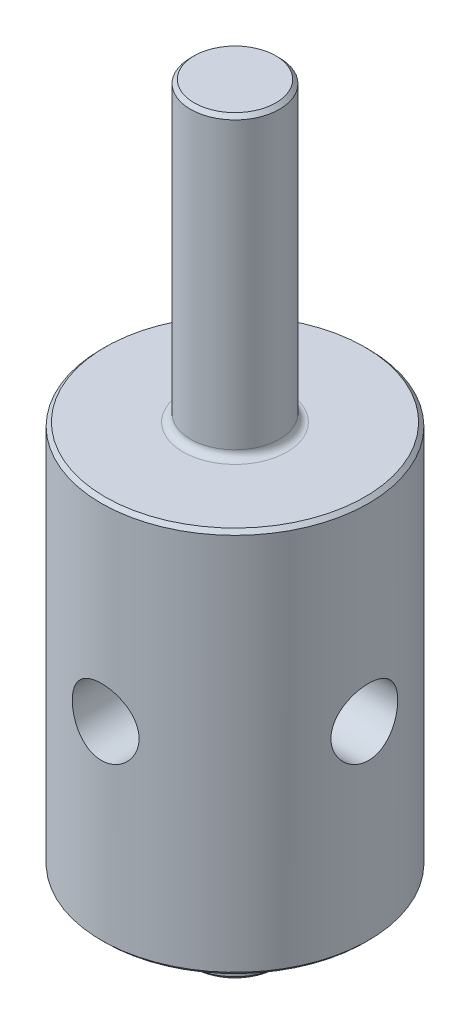
SolidWorks part; units mm, degrees
material "AISI 316 Barra de aço inoxidável recozido (SS)"
ref_plane "Plano frontal" through (0, 0, 0) normal (0, 0, 1) x (1, 0, 0)
ref_plane "Plano superior" through (0, 0, 0) normal (0, 1, 0) x (1, 0, 0)
ref_plane "Plano direito" through (0, 0, 0) normal (1, 0, 0) x (0, 0, -1)
sketch "Esboço1" plane through (0, 0, 0) normal (0, 0, 1) x (1, 0, 0)
  line L0 (0, 0) -> (0, 26.74) construction
  line L1 (0, 0) -> (9, 0) construction
  line L2 (0, 33) -> (3, 33)
  line L3 (3, 13) -> (3, 33)
  line L4 (9, 13) -> (3, 13)
  line L11 (9, 13) -> (9, -13)
  line L12 (0, 33) -> (0, 0)
  line L17 (3, -13) -> (9, -13)
  line L18 (3, -17.5) -> (3, -13)
  line L21 (3, -17.5) -> (0, -17.5)
  line L22 (0, -17.5) -> (0, 0)
  point P16 (9, 0)
  dimension "D1" = 6
  dimension "D2" = 6
  dimension "D5" = 18
  dimension "D6" = 20
  dimension "D7" = 26
  dimension "D9" = 4.5
revolve "Revolução1" add sketch "Esboço1" angle 360 about L0
ref_plane "Plano1" through (-9, 0, 0) normal (-1, 0, 0) x (0, 0, 1)
ref_plane "Plano2" through (9, 0, 0) normal (1, 0, 0) x (0, 0, -1)
sketch "Esboço2" plane through (-9, 0, 0) normal (-1, 0, 0) x (0, 0, 1)
  circle A0 centre (0, 0) radius 2.25
  dimension "D1" = 4.5
extrude "Corte-extrusão2" [suppressed] cut sketch "Esboço2" against normal through all
hole_wizard "Furo de diâmetro Ø4.5 (4.5)2" positions "3DSketch2" profile "Esboço9" hole size "Ø4.5" standard "Ansi Metric" end condition through all
sketch3d "3DSketch2"
  point P0 (-9, 0, 0)
sketch "Esboço9" plane through (-9, 0, 0) normal (0, 1, 0) x (0, 0, 1)
  line L0 (0, 0) -> (0, 18)
  line L1 (0, 18) -> (2.25, 18)
  line L2 (2.25, 18) -> (2.25, 0)
  line L5 (2.25, 0) -> (0, 0)
  line L11 (0, -6.35) -> (0, 107.95) construction
  dimension "Thru Hole Dia." = 4.5
  dimension "Thru Hole Depth" = 18
hole_wizard "Furo de diâmetro Ø4.5 (4.5)1" positions "3DSketch1" profile "Esboço8" hole size "Ø4.5" standard "Ansi Metric"
sketch3d "3DSketch1"
  point P0 (0, 0, 0)
  point P3 (0, 0, 0)
  point P5 (0, 0, 9)
sketch "Esboço8" plane through (0, 0, 9) normal (1, 0, 0) x (0, -1, 0)
  line L0 (0, 0) -> (0, 9)
  line L1 (0, 9) -> (2.25, 9)
  line L2 (2.25, 9) -> (2.25, 0)
  line L5 (2.25, 0) -> (0, 0)
  line L11 (0, -6.35) -> (0, 107.95) construction
  dimension "Thru Hole Dia." = 4.5
  dimension "Thru Hole Depth" = 9
sketch "Esboço4" [suppressed] plane through (0, 0, 0) normal (0, 1, 0) x (1, 0, 0)
  line L0 (9, 0) -> (-9, 0)
  line L1 (0, 0) -> (-7.7942, -4.5) construction
  line L2 (9, 0) -> (-7.7942, -4.5)
  arc A0 (8.7142, -2.25) -> (8.7142, 2.25) centre (0, 0) ccw construction
  circle A1 centre (0, 0) radius 9 construction
  dimension "D1" = 30
ref_plane "Plano3" [suppressed] through (-7.7942, 0, 4.5) normal (-0.9659, 0, 0.2588) x (0.2588, 0, 0.9659)
sketch "Esboço7" [suppressed] plane through (-7.7942, 0, 4.5) normal (-0.9659, 0, 0.2588) x (0.2588, 0, 0.9659)
  circle A0 centre (0, 0) radius 2.25
  dimension "D1" = 4.5
extrude "Corte-extrusão6" [suppressed] cut sketch "Esboço7" against normal through all both and the other way through all
sketch "Sketch1" [suppressed] plane through (0, 0, 0) normal (0, 1, 0) x (1, 0, 0)
  line L0 (9, 0) -> (-10.8444, 0)
  line L1 (-10.8444, 0) -> (-10.4288, -5.2059)
  line L2 (-10.4288, -5.2059) -> (9, 0)
  line L3 (9, 0) -> (-7.7942, -4.5) construction
extrude "Cut-Extrude1" [suppressed] cut sketch "Sketch1" against normal mid plane 4.5
sketch "Sketch2" plane through (0, 0, 0) normal (0, 0, 1) x (1, 0, 0)
  line L0 (8.5, -13) -> (9, 13)
  line L1 (-9, -13) -> (9, -13) construction
  line L2 (9, -9.9) -> (9, 9.9) construction
  line L3 (9, 13) -> (-9, 13) construction
  line L4 (9, 13) -> (9, -13)
  line L5 (9, -13) -> (8.5, -13)
  dimension "D1" = 0.5
revolve "Cut-Revolve1" [suppressed] cut sketch "Sketch2" angle 360
fillet "Fillet1" radius 0.5 2 edges at (0, -13, -3) (0, 13, -3)
chamfer "Chamfer1" distance 0.25 angle 45 2 edges at (0, -17.5, -3) (0, 33, -3)
chamfer "Chamfer3" [suppressed] distance 0.25 angle 45
chamfer "Chamfer4" distance 0.25 angle 45 2 edges at (0, -13, -9) (0, 13, -9)
